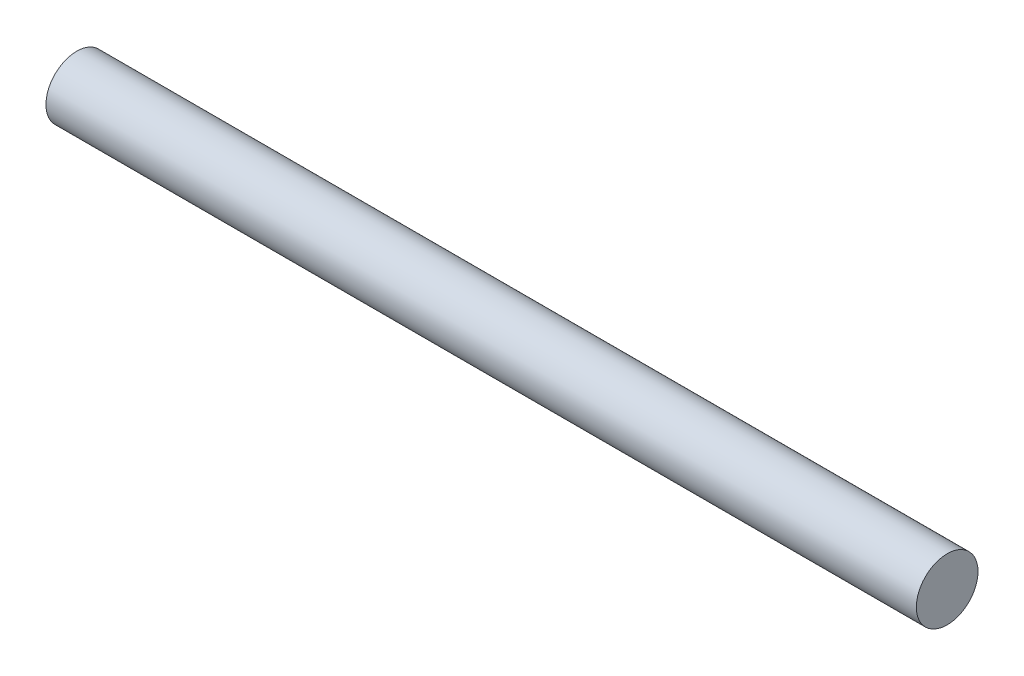
SolidWorks part; units mm, degrees
material "1023 Carbon Steel Sheet (SS)"
ref_plane "Front Plane" through (0, 0, 0) normal (0, 0, 1) x (1, 0, 0)
ref_plane "Top Plane" through (0, 0, 0) normal (0, 1, 0) x (1, 0, 0)
ref_plane "Right Plane" through (0, 0, 0) normal (1, 0, 0) x (0, 0, -1)
sketch "Sketch1" plane through (0, 0, 0) normal (1, 0, 0) x (0, 0, -1)
  circle A0 centre (0, 0) radius 10.795
  dimension "D1" = 21.59
extrude "Boss-Extrude1" add sketch "Sketch1" along normal mid plane 304.8
